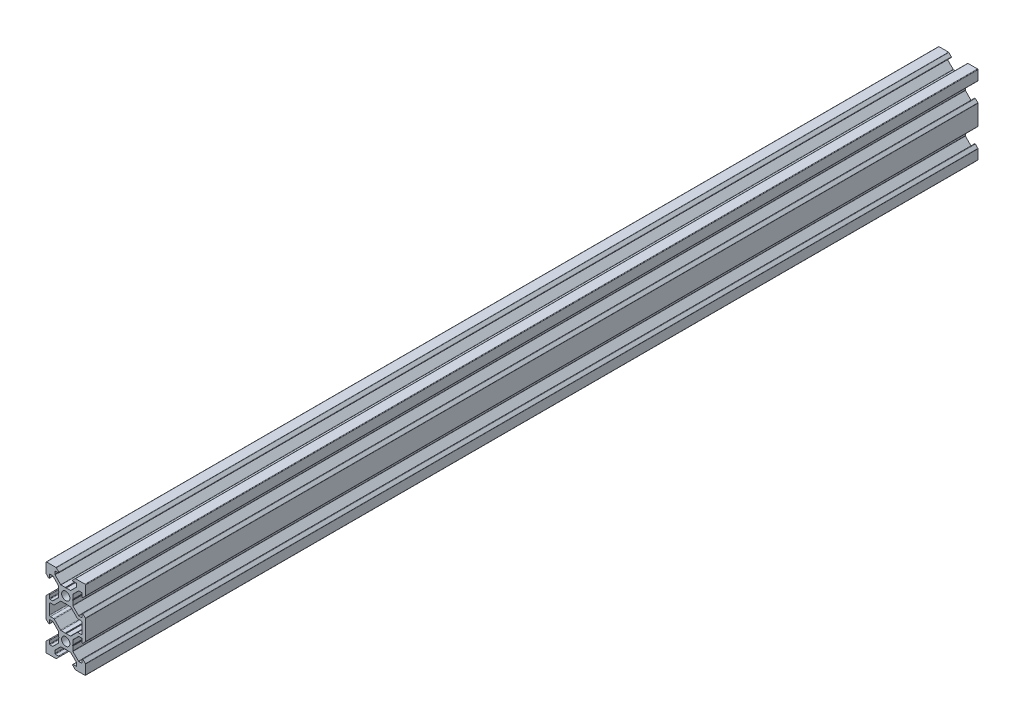
SolidWorks part; units mm, degrees
ref_plane "Front Plane" through (0, 0, 0) normal (0, 0, 1) x (1, 0, 0)
ref_plane "Top Plane" through (0, 0, 0) normal (0, 1, 0) x (1, 0, 0)
ref_plane "Right Plane" through (0, 0, 0) normal (1, 0, 0) x (0, 0, -1)
sketch "Sketch1" plane through (0, 0, 0) normal (0, 0, 1) x (1, 0, 0)
  line L0 (3.5607, 3.5607) -> (10.6317, 10.6317) construction
  line L1 (2.5, -3.5607) -> (-2.5, -3.5607)
  line L2 (3.5607, -2.5) -> (3.5607, 2.5)
  line L3 (2.5, 3.5607) -> (-2.5, 3.5607)
  line L4 (-3.5607, -2.5) -> (-3.5607, 2.5)
  line L5 (3.5607, -3.5607) -> (-3.5607, 3.5607) construction
  line L6 (3.5607, 3.5607) -> (-3.5607, -3.5607) construction
  line L7 (2.5, 3.5607) -> (5.5, 6.5607)
  line L8 (5.5, 6.5607) -> (5.5, 8.2521)
  line L9 (5.5, 8.2521) -> (3.1, 8.2521)
  line L10 (3.1, 8.2521) -> (4.8479, 10)
  line L11 (4.8479, 10) -> (10, 10)
  line L12 (3.5607, 2.5) -> (6.5607, 5.5)
  line L13 (6.5607, 5.5) -> (8.2521, 5.5)
  line L14 (8.2521, 5.5) -> (8.2521, 3.1)
  line L15 (8.2521, 3.1) -> (10, 4.8479)
  line L16 (10, 4.8479) -> (10, 10)
  line L17 (0, -55) -> (0, 55) construction
  line L18 (-3.5607, 3.5607) -> (-10.6317, 10.6317) construction
  line L19 (-10, 4.8479) -> (-10, 10)
  line L20 (-8.2521, 3.1) -> (-10, 4.8479)
  line L21 (-8.2521, 5.5) -> (-8.2521, 3.1)
  line L22 (-6.5607, 5.5) -> (-8.2521, 5.5)
  line L23 (-3.5607, 2.5) -> (-6.5607, 5.5)
  line L24 (-4.8479, 10) -> (-10, 10)
  line L25 (-3.1, 8.2521) -> (-4.8479, 10)
  line L26 (-5.5, 8.2521) -> (-3.1, 8.2521)
  line L27 (-5.5, 6.5607) -> (-5.5, 8.2521)
  line L28 (-2.5, 3.5607) -> (-5.5, 6.5607)
  line L29 (-8.2521, -7) -> (-5.9393, -7)
  line L30 (55, 0) -> (-55, 0) construction
  line L31 (-3.5607, -3.5607) -> (-10.6317, -10.6317) construction
  line L32 (3.5607, -3.5607) -> (10.6317, -10.6317) construction
  line L33 (-2.5, -3.5607) -> (-5.5, -6.5607)
  line L34 (-5.5, -6.5607) -> (-5.9393, -7)
  line L35 (5.5, -6.5607) -> (5.9393, -7)
  line L36 (8.2521, -7) -> (5.9393, -7)
  line L37 (-12.2633, -10) -> (14.5346, -10) construction
  line L38 (-3.5607, -2.5) -> (-6.5607, -5.5)
  line L39 (-6.5607, -5.5) -> (-8.2521, -5.5)
  line L40 (-8.2521, -5.5) -> (-8.2521, -3.1)
  line L41 (-8.2521, -3.1) -> (-10, -4.8479)
  line L42 (-10, -4.8479) -> (-10, -7)
  line L43 (10, -4.8479) -> (10, -7)
  line L44 (8.2521, -3.1) -> (10, -4.8479)
  line L45 (8.2521, -5.5) -> (8.2521, -3.1)
  line L46 (6.5607, -5.5) -> (8.2521, -5.5)
  line L47 (3.5607, -2.5) -> (6.5607, -5.5)
  line L48 (-3.5607, -23.5607) -> (-10.6317, -30.6317) construction
  line L49 (3.5607, -23.5607) -> (-3.5607, -16.4393) construction
  line L50 (3.5607, -16.4393) -> (-3.5607, -23.5607) construction
  line L51 (3.5607, -23.5607) -> (10.6317, -30.6317) construction
  line L52 (2.5, -3.5607) -> (5.5, -6.5607)
  line L53 (2.5, -16.4393) -> (5.5, -13.4393)
  line L54 (3.5607, -17.5) -> (6.5607, -14.5)
  line L55 (6.5607, -14.5) -> (8.2521, -14.5)
  line L56 (8.2521, -14.5) -> (8.2521, -16.9)
  line L57 (8.2521, -16.9) -> (10, -15.1521)
  line L58 (10, -15.1521) -> (10, -13)
  line L59 (-10, -15.1521) -> (-10, -13)
  line L60 (-8.2521, -16.9) -> (-10, -15.1521)
  line L61 (-8.2521, -14.5) -> (-8.2521, -16.9)
  line L62 (-6.5607, -14.5) -> (-8.2521, -14.5)
  line L63 (-3.5607, -17.5) -> (-6.5607, -14.5)
  line L64 (8.2521, -13) -> (5.9393, -13)
  line L65 (5.5, -13.4393) -> (5.9393, -13)
  line L66 (-5.5, -13.4393) -> (-5.9393, -13)
  line L67 (-2.5, -16.4393) -> (-5.5, -13.4393)
  line L68 (-8.2521, -13) -> (-5.9393, -13)
  line L69 (-2.5, -23.5607) -> (-5.5, -26.5607)
  line L70 (-5.5, -26.5607) -> (-5.5, -28.2521)
  line L71 (-5.5, -28.2521) -> (-3.1, -28.2521)
  line L72 (-3.1, -28.2521) -> (-4.8479, -30)
  line L73 (-4.8479, -30) -> (-10, -30)
  line L74 (-3.5607, -22.5) -> (-6.5607, -25.5)
  line L75 (-6.5607, -25.5) -> (-8.2521, -25.5)
  line L76 (-8.2521, -25.5) -> (-8.2521, -23.1)
  line L77 (-8.2521, -23.1) -> (-10, -24.8479)
  line L78 (-10, -24.8479) -> (-10, -30)
  line L79 (10, -24.8479) -> (10, -30)
  line L80 (8.2521, -23.1) -> (10, -24.8479)
  line L81 (8.2521, -25.5) -> (8.2521, -23.1)
  line L82 (6.5607, -25.5) -> (8.2521, -25.5)
  line L83 (3.5607, -22.5) -> (6.5607, -25.5)
  line L84 (4.8479, -30) -> (10, -30)
  line L85 (3.1, -28.2521) -> (4.8479, -30)
  line L86 (5.5, -28.2521) -> (3.1, -28.2521)
  line L87 (5.5, -26.5607) -> (5.5, -28.2521)
  line L88 (2.5, -23.5607) -> (5.5, -26.5607)
  line L89 (-3.5607, -17.5) -> (-3.5607, -22.5)
  line L90 (2.5, -23.5607) -> (-2.5, -23.5607)
  line L91 (3.5607, -17.5) -> (3.5607, -22.5)
  line L92 (2.5, -16.4393) -> (-2.5, -16.4393)
  line L93 (-10, -7) -> (-10, -13)
  line L94 (-8.2521, -13) -> (-8.2521, -7)
  line L95 (8.2521, -13) -> (8.2521, -7)
  line L96 (10, -7) -> (10, -13)
  circle A0 centre (0, 0) radius 2.1
  circle A1 centre (0, -20) radius 2.1
  point P0 (0, 0)
  point P102 (0, -20)
  dimension "D10" = 4.2
  dimension "D11" = 4.2
  dimension "D1" = 1.5
  dimension "D2" = 10
  dimension "D3" = 20
  dimension "D4" = 6.2
  dimension "D5" = 11
  dimension "D6" = 45
  dimension "D7" = 1.5
  dimension "D8" = 10
  dimension "D9" = 5
extrude "Boss-Extrude1" add sketch "Sketch1" along normal blind 452
fillet "Fillet1" radius 0.25 64 edges at (5.5, 6.5607, 226) (5.5, 8.2521, 226) (3.1, 8.2521, 226) (4.8479, 10, 226) (10, 10, 226) (10, 4.8479, 226) (8.2521, 3.1, 226) (8.2521, 5.5, 226) (6.5607, 5.5, 226) (3.5607, 2.5, 226) (3.5607, -2.5, 226) (6.5607, -5.5, 226) (8.2521, -5.5, 226) (8.2521, -3.1, 226) (10, -4.8479, 226) (10, -15.1521, 226) (8.2521, -16.9, 226) (8.2521, -14.5, 226) (6.5607, -14.5, 226) (3.5607, -17.5, 226) (3.5607, -22.5, 226) (6.5607, -25.5, 226) (8.2521, -25.5, 226) (8.2521, -23.1, 226) (10, -24.8479, 226) (10, -30, 226) (4.8479, -30, 226) (3.1, -28.2521, 226) (5.5, -28.2521, 226) (5.5, -26.5607, 226) (2.5, -23.5607, 226) (-2.5, -23.5607, 226) (-5.5, -26.5607, 226) (-5.5, -28.2521, 226) (-3.1, -28.2521, 226) (-4.8479, -30, 226) (-10, -30, 226) (-10, -24.8479, 226) (-8.2521, -23.1, 226) (-8.2521, -25.5, 226) (-6.5607, -25.5, 226) (-3.5607, -22.5, 226) (-3.5607, -17.5, 226) (-6.5607, -14.5, 226) (-8.2521, -14.5, 226) (-8.2521, -16.9, 226) (-10, -15.1521, 226) (-10, -4.8479, 226) (-8.2521, -3.1, 226) (-8.2521, -5.5, 226) (-6.5607, -5.5, 226) (-3.5607, -2.5, 226) (-3.5607, 2.5, 226) (-6.5607, 5.5, 226) (-8.2521, 5.5, 226) (-8.2521, 3.1, 226) (-10, 4.8479, 226) (-10, 10, 226) (-4.8479, 10, 226) (-5.5, 8.2521, 226) (-5.5, 6.5607, 226) (-2.5, 3.5607, 226) (2.5, 3.5607, 226) (-3.1, 8.2521, 226)
fillet "Fillet2" radius 0.5 12 edges at (-5.9393, -7, 226) (-8.2521, -7, 226) (-8.2521, -13, 226) (-5.9393, -13, 226) (-2.5, -16.4393, 226) (2.5, -16.4393, 226) (8.2521, -7, 226) (5.9393, -7, 226) (2.5, -3.5607, 226) (-2.5, -3.5607, 226) (5.9393, -13, 226) (8.2521, -13, 226)
sketch "Sketch2" plane through (0, 0, 452) normal (0, 0, 1) x (1, 0, 0)
  line L4 (0, 3.5607) -> (0, 3.1447) construction
  line L5 (2.3964, 3.5607) -> (-2.3964, 3.5607) construction
  line L6 (0, 3.399) -> (-0.2423, 3.5607)
  line L7 (0, 3.399) -> (0.2423, 3.5607)
  line L8 (-0.2423, 3.5607) -> (0.2423, 3.5607)
  line L9 (55, 0) -> (-55, 0) construction
  line L10 (0, -3.5607) -> (0, -3.1447) construction
  line L11 (0, -3.399) -> (0.2423, -3.5607)
  line L12 (0, -3.399) -> (-0.2423, -3.5607)
  line L13 (-0.2423, -3.5607) -> (0.2423, -3.5607)
  line L14 (0, 0) -> (-4.0856, 4.0856) construction
  line L15 (-8.2521, -10) -> (4.1581, -10) construction
  line L16 (-8.2521, -7.5) -> (-8.2521, -12.5) construction
  line L17 (3.5607, 0) -> (3.1447, 0) construction
  line L18 (3.5607, 0.2423) -> (3.5607, -0.2423)
  line L19 (3.399, 0) -> (3.5607, 0.2423)
  line L20 (3.399, 0) -> (3.5607, -0.2423)
  line L21 (-3.5607, 0) -> (-3.1447, 0) construction
  line L22 (-3.5607, 0.2423) -> (-3.5607, -0.2423)
  line L23 (-3.399, 0) -> (-3.5607, -0.2423)
  line L24 (-3.399, 0) -> (-3.5607, 0.2423)
  line L25 (-3.5607, -20) -> (-3.1447, -20) construction
  line L26 (3.5607, -20) -> (3.1447, -20) construction
  line L27 (0, -20) -> (-4.0856, -24.0856) construction
  line L28 (0, -16.4393) -> (0, -16.8553) construction
  line L29 (0, -23.5607) -> (0, -23.1447) construction
  line L30 (-3.399, -20) -> (-3.5607, -20.2423)
  line L31 (-3.399, -20) -> (-3.5607, -19.7577)
  line L32 (-3.5607, -20.2423) -> (-3.5607, -19.7577)
  line L33 (3.399, -20) -> (3.5607, -19.7577)
  line L34 (3.399, -20) -> (3.5607, -20.2423)
  line L35 (3.5607, -20.2423) -> (3.5607, -19.7577)
  line L36 (-0.2423, -16.4393) -> (0.2423, -16.4393)
  line L37 (0, -16.601) -> (-0.2423, -16.4393)
  line L38 (0, -16.601) -> (0.2423, -16.4393)
  line L39 (-0.2423, -23.5607) -> (0.2423, -23.5607)
  line L40 (0, -23.399) -> (0.2423, -23.5607)
  line L41 (0, -23.399) -> (-0.2423, -23.5607)
extrude "Cut-Extrude1" cut sketch "Sketch2" against normal through all
